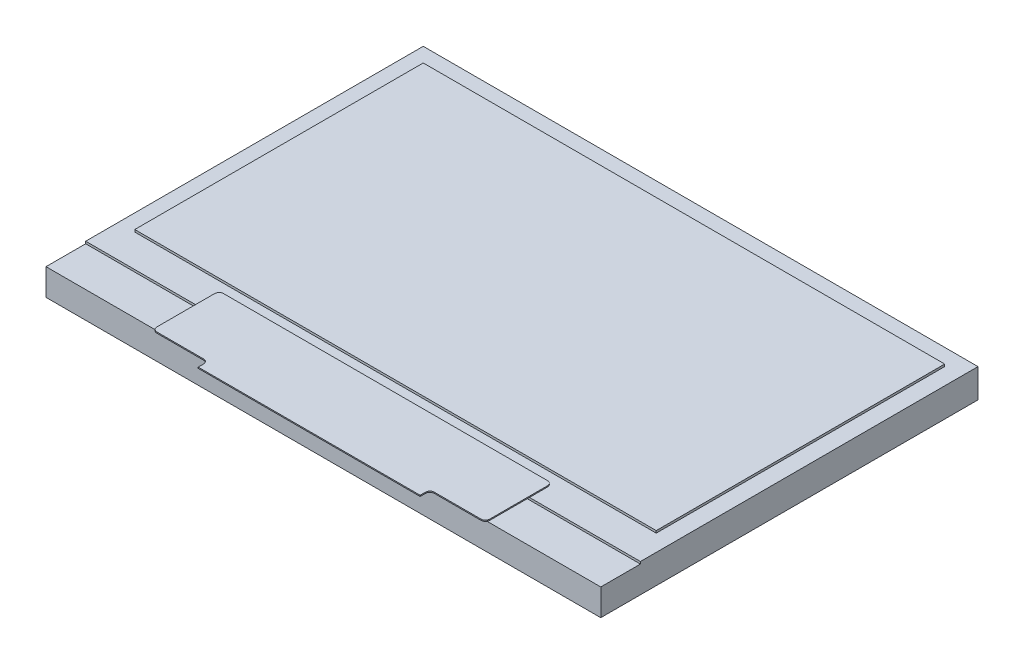
SolidWorks part; units mm, degrees
ref_plane "Front Plane" through (0, 0, 0) normal (0, 0, 1) x (1, 0, 0)
ref_plane "Top Plane" through (0, 0, 0) normal (0, 1, 0) x (1, 0, 0)
ref_plane "Right Plane" through (0, 0, 0) normal (1, 0, 0) x (0, 0, -1)
sketch "Sketch3" plane through (0, 0, 0) normal (0, 1, 0) x (1, 0, 0)
  line L0 (-12.5, -4.42) -> (12.5, -4.42)
  line L4 (-12.5, -21.42) -> (12.5, -21.42)
  line L5 (-12.5, -4.42) -> (-12.5, -21.42)
  line L6 (12.5, -4.42) -> (12.5, -21.42)
  line L7 (0, 0) -> (0, -25.8) construction
  dimension "D2" = 17
  dimension "D3" = 25
extrude "Boss-Extrude3" add sketch "Sketch3" along normal blind 1.3
sketch "Sketch4" plane through (-12.5, 0, 0) normal (-1, 0, 0) x (0, 0, 1)
  line L0 (4.42, 1.3) -> (4.42, 0) construction
  line L1 (23.68, 1.2) -> (19.6327, 1.2)
  line L2 (23.68, 1.2) -> (23.68, 1.85)
  line L3 (23.68, 1.85) -> (19.6327, 1.85)
  line L4 (19.6327, 1.2) -> (19.6327, 1.85)
  point P5 (4.42, 0.65)
  dimension "D1" = 0.65
  dimension "D2" = 15.26
extrude "Cut-Extrude1" cut sketch "Sketch4" against normal blind 30.3
sketch "Sketch6" plane through (0, 1.3, 0) normal (0, 1, 0) x (1, 0, 0)
  line L1 (11.75, -5.17) -> (-11.75, -5.17)
  line L2 (11.75, -5.17) -> (11.75, -18.17)
  line L3 (11.75, -18.17) -> (-11.75, -18.17)
  line L4 (-11.75, -5.17) -> (-11.75, -18.17)
  line L5 (12.5, -4.42) -> (-12.5, -4.42) construction
  dimension "D1" = 0.75
  dimension "D2" = 23.5
  dimension "D4" = 13
extrude "Boss-Extrude4" add sketch "Sketch6" along normal blind 0.1
sketch "Sketch10" plane through (0, 1.3, 0) normal (0, 1, 0) x (1, 0, 0)
  line L0 (0, -23.68) -> (0, -18.17) construction
  line L2 (-11.75, -18.17) -> (11.75, -18.17) construction
  line L3 (-5, -21.82) -> (-5, -22.06)
  line L4 (-7.3, -21.62) -> (-5.2, -21.62)
  line L5 (-7.5, -21.42) -> (-7.5, -18.82)
  line L6 (-7.3, -18.62) -> (7.3, -18.62)
  line L7 (7.5, -21.42) -> (7.5, -18.82)
  line L8 (-7.5, -21.62) -> (7.5, -18.62) construction
  line L9 (-7.5, -18.62) -> (7.5, -21.62) construction
  line L10 (-5, -22.06) -> (5, -22.06)
  line L11 (5, -22.06) -> (5, -21.82)
  line L12 (5.2, -21.62) -> (7.3, -21.62)
  line L13 (-11.75, -18.17) -> (11.75, -18.17) construction
  arc A0 (7.3, -18.62) -> (7.5, -18.82) centre (7.3, -18.82) cw
  arc A1 (7.3, -21.62) -> (7.5, -21.42) centre (7.3, -21.42) ccw
  arc A2 (5, -21.82) -> (5.2, -21.62) centre (5.2, -21.82) cw
  arc A3 (-5, -21.82) -> (-5.2, -21.62) centre (-5.2, -21.82) ccw
  arc A4 (-7.3, -21.62) -> (-7.5, -21.42) centre (-7.3, -21.42) cw
  arc A5 (-7.5, -18.82) -> (-7.3, -18.62) centre (-7.3, -18.82) cw
  point P6 (0, -20.12)
  point P25 (5, -21.62)
  point P28 (-5, -21.62)
  dimension "D7" = 0.2
  dimension "D1" = 15
  dimension "D2" = 3
  dimension "D3" = 10
  dimension "D5" = 0.45
  dimension "D6" = 0.44
extrude "Boss-Extrude6" add sketch "Sketch10" along normal blind 0.05
